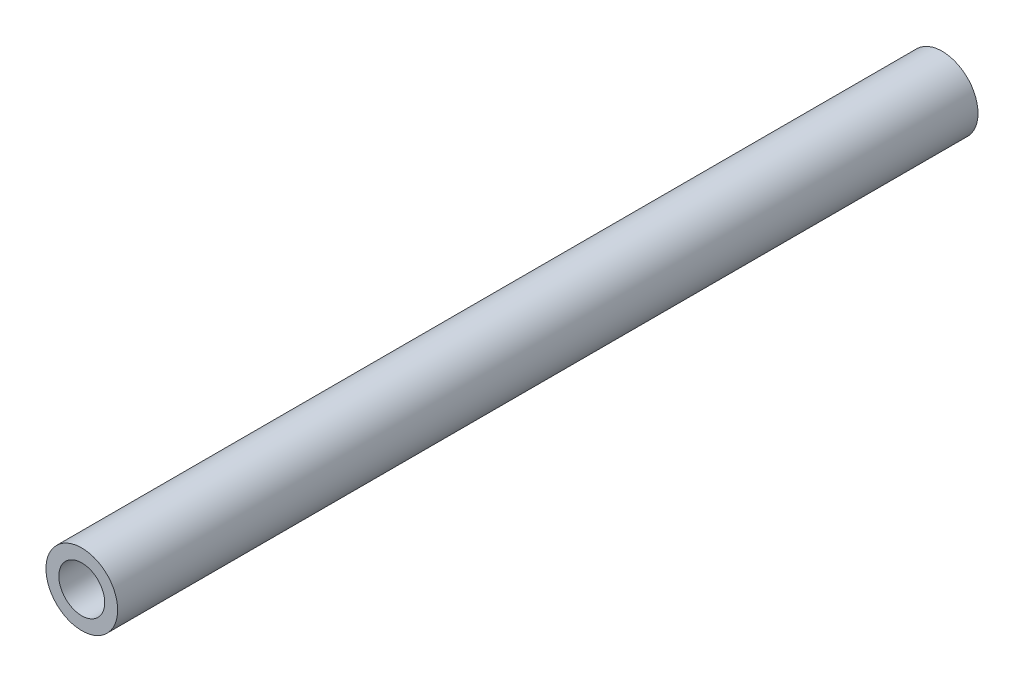
SolidWorks part; units mm, degrees
ref_plane "Front" through (0, 0, 0) normal (0, 0, 1) x (1, 0, 0)
ref_plane "Top" through (0, 0, 0) normal (0, 1, 0) x (1, 0, 0)
ref_plane "Right" through (0, 0, 0) normal (1, 0, 0) x (0, 0, -1)
sketch "Sketch1" plane through (0, 0, 0) normal (0, 0, 1) x (1, 0, 0)
  circle A0 centre (0, 0) radius 1.6
  circle A1 centre (0, 0) radius 2.5
extrude "Boss-Extrude1" add sketch "Sketch1" along normal blind 60
